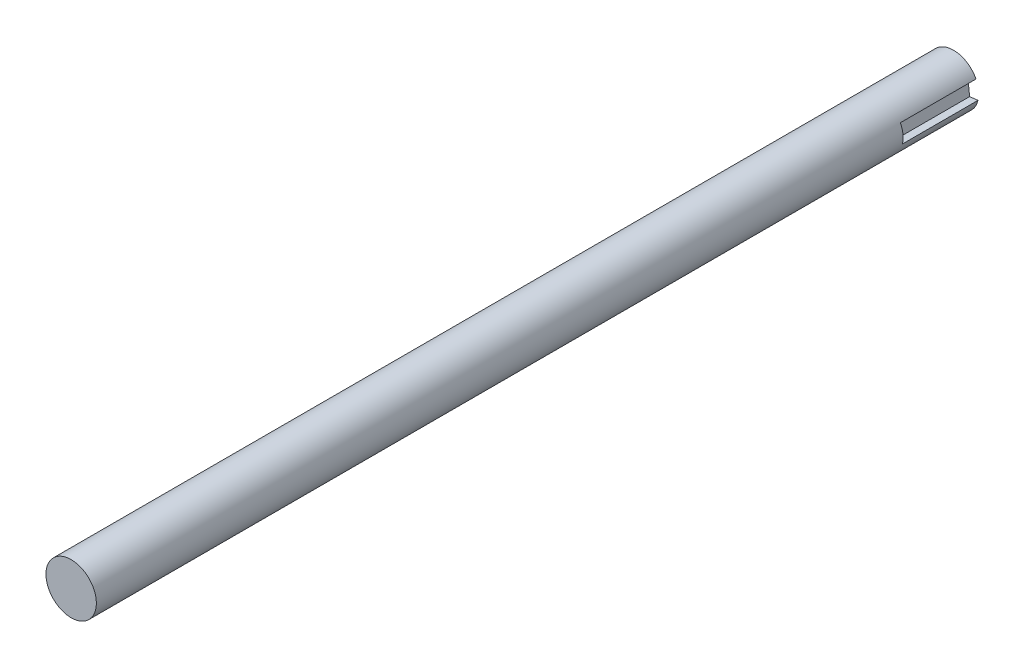
SolidWorks part; units mm, degrees
ref_plane "Front Plane" through (0, 0, 0) normal (0, 0, 1) x (1, 0, 0)
ref_plane "Top Plane" through (0, 0, 0) normal (0, 1, 0) x (1, 0, 0)
ref_plane "Right Plane" through (0, 0, 0) normal (1, 0, 0) x (0, 0, -1)
sketch "Sketch1" plane through (0, 0, 0) normal (0, 0, 1) x (1, 0, 0)
  circle A0 centre (0, 0) radius 5
  dimension "D1" = 10
extrude "Boss-Extrude1" add sketch "Sketch1" along normal blind 72 and the other way blind 103
sketch "Sketch2" plane through (0, 0, -103) normal (0, 0, -1) x (-1, 0, 0)
  line L0 (-4.8556, -1.1931) -> (-3.1962, -1.3814)
  line L1 (-6.8428, -0.9676) -> (-4.8556, -1.1931) construction
  line L2 (-3.1962, -1.3814) -> (-2.8022, 2.091)
  line L3 (-4.4581, 2.264) -> (-2.8022, 2.091)
  circle A0 centre (0, 0) radius 5 construction
  arc A1 (-4.8556, -1.1931) -> (-4.4581, 2.264) centre (0, 0) cw
extrude "Cut-Extrude1" cut sketch "Sketch2" against normal blind 15
